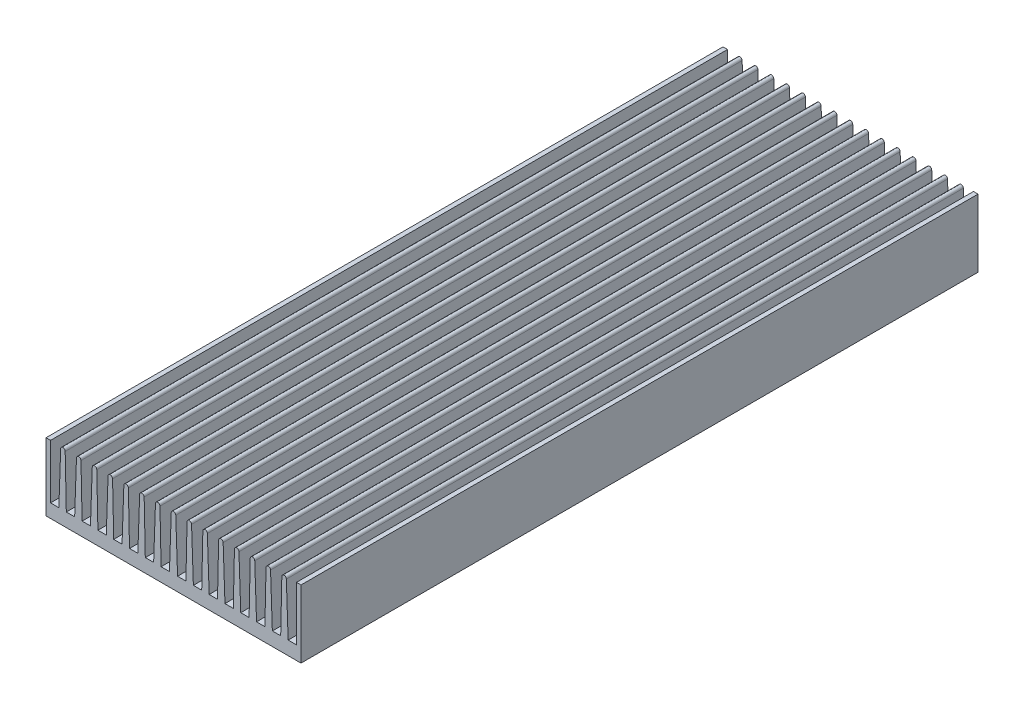
SolidWorks part; units mm, degrees
ref_plane "Plano frontal" through (0, 0, 0) normal (0, 0, 1) x (1, 0, 0)
ref_plane "Plano superior" through (0, 0, 0) normal (0, 1, 0) x (1, 0, 0)
ref_plane "Plano direito" through (0, 0, 0) normal (1, 0, 0) x (0, 0, -1)
sketch "Esboço1" plane through (0, 0, 0) normal (0, 0, 1) x (1, 0, 0)
  line L3 (0, 0) -> (-113, 0)
  line L102 (-76, 6) -> (-72.3, 6)
  line L103 (-83, 6) -> (-79.3, 6)
  line L104 (-86.3, 6) -> (-90, 6)
  line L115 (-56.5, 0) -> (-56.5, 30) construction
  line L116 (-113, 30) -> (15.3408, 30) construction
  line L146 (-86.3, 6) -> (-85.5, 29)
  line L147 (-83.5, 29) -> (-83, 6)
  line L148 (-85.5, 29) -> (-83.5, 29) construction
  line L149 (-90, 6) -> (-90.5, 29)
  line L150 (-92.5, 29) -> (-93.3, 6)
  line L151 (-48.5, 29) -> (-50.5, 29) construction
  line L152 (-93.3, 6) -> (-97, 6)
  line L153 (-97, 6) -> (-97.5, 29)
  line L154 (-99.5, 29) -> (-100.3, 6)
  line L155 (-79.3, 6) -> (-78.5, 29)
  line L156 (-76.5, 29) -> (-76, 6)
  line L161 (-78.5, 29) -> (-76.5, 29) construction
  line L162 (-72.3, 6) -> (-71.5, 29)
  line L163 (-100.3, 6) -> (-104, 6)
  line L164 (-71.5, 29) -> (-69.5, 29) construction
  line L165 (-69.5, 29) -> (-69, 6)
  line L167 (-104, 6) -> (-104.5, 29)
  line L169 (-8.5, 29) -> (-6.5, 29) construction
  line L170 (-90.5, 29) -> (-92.5, 29) construction
  line L171 (-97.5, 29) -> (-99.5, 29) construction
  line L172 (-104.5, 29) -> (-106.5, 29) construction
  line L173 (-15.5, 29) -> (-13.5, 29) construction
  line L174 (-22.5, 29) -> (-20.5, 29) construction
  line L175 (-107.3, 6) -> (-106.5, 29)
  line L176 (-113, 0) -> (-113, 30)
  line L177 (-113, 30) -> (-111, 30)
  line L178 (-111, 30) -> (-111, 6)
  line L179 (-111, 6) -> (-107.3, 6)
  line L181 (-57.5, 29) -> (-55.5, 29) construction
  line L183 (-69, 6) -> (-65.3, 6)
  line L184 (-65.3, 6) -> (-64.5, 29)
  line L185 (-64.5, 29) -> (-62.5, 29) construction
  line L186 (-62.5, 29) -> (-62, 6)
  line L187 (-62, 6) -> (-58.3, 6)
  line L188 (-58.3, 6) -> (-57.5, 29)
  line L189 (-41.5, 29) -> (-43.5, 29) construction
  line L190 (-34.5, 29) -> (-36.5, 29) construction
  line L191 (-27.5, 29) -> (-29.5, 29) construction
  line L192 (-54.7, 6) -> (-55.5, 29)
  line L193 (-51, 6) -> (-54.7, 6)
  line L194 (-50.5, 29) -> (-51, 6)
  line L195 (-47.7, 6) -> (-48.5, 29)
  line L196 (-44, 6) -> (-47.7, 6)
  line L197 (-2, 6) -> (-5.7, 6)
  line L198 (-2, 30) -> (-2, 6)
  line L199 (0, 30) -> (-2, 30)
  line L200 (0, 0) -> (0, 30)
  line L201 (-5.7, 6) -> (-6.5, 29)
  line L202 (-9, 6) -> (-8.5, 29)
  line L203 (-43.5, 29) -> (-44, 6)
  line L204 (-12.7, 6) -> (-9, 6)
  line L205 (-40.7, 6) -> (-41.5, 29)
  line L206 (-36.5, 29) -> (-37, 6)
  line L207 (-33.7, 6) -> (-34.5, 29)
  line L208 (-13.5, 29) -> (-12.7, 6)
  line L209 (-16, 6) -> (-15.5, 29)
  line L210 (-19.7, 6) -> (-16, 6)
  line L211 (-20.5, 29) -> (-19.7, 6)
  line L212 (-23, 6) -> (-22.5, 29)
  line L213 (-29.5, 29) -> (-30, 6)
  line L214 (-26.7, 6) -> (-27.5, 29)
  line L215 (-26.7, 6) -> (-23, 6)
  line L216 (-30, 6) -> (-33.7, 6)
  line L217 (-37, 6) -> (-40.7, 6)
  arc A4 (-85.5, 29) -> (-83.5, 29) centre (-84.5, 29) cw
  arc A6 (-78.5, 29) -> (-76.5, 29) centre (-77.5, 29) cw
  arc A8 (-71.5, 29) -> (-69.5, 29) centre (-70.5, 29) cw
  arc A20 (-90.5, 29) -> (-92.5, 29) centre (-91.5, 29) ccw
  arc A21 (-99.5, 29) -> (-97.5, 29) centre (-98.5, 29) cw
  arc A22 (-106.5, 29) -> (-104.5, 29) centre (-105.5, 29) cw
  arc A29 (-57.5, 29) -> (-55.5, 29) centre (-56.5, 29) cw
  arc A30 (-64.5, 29) -> (-62.5, 29) centre (-63.5, 29) cw
  arc A31 (-48.5, 29) -> (-50.5, 29) centre (-49.5, 29) ccw
  arc A32 (-6.5, 29) -> (-8.5, 29) centre (-7.5, 29) ccw
  arc A33 (-13.5, 29) -> (-15.5, 29) centre (-14.5, 29) ccw
  arc A34 (-22.5, 29) -> (-20.5, 29) centre (-21.5, 29) cw
  arc A35 (-41.5, 29) -> (-43.5, 29) centre (-42.5, 29) ccw
  arc A36 (-34.5, 29) -> (-36.5, 29) centre (-35.5, 29) ccw
  arc A37 (-27.5, 29) -> (-29.5, 29) centre (-28.5, 29) ccw
  point P43 (-56.5, 30)
  dimension "D2" = 1
  dimension "D1" = 7
  dimension "D3" = 3.7
  dimension "D4" = 2
  dimension "D5" = 6
  dimension "D6" = 113
  dimension "D8" = 30
extrude "Ressalto-extrusão1" add sketch "Esboço1" along normal blind 300
sketch "Esboço2" plane through (0, 0, 300) normal (0, 0, 1) x (1, 0, 0)
  line L1 (-100.3, 6) -> (-104, 6) construction
  line L5 (-102.5538, 0) -> (-10.4462, 0) construction
  line L23 (-9.4462, 1.7321) -> (-10.4462, 0)
  line L27 (-113, 0) -> (0, 0) construction
  line L28 (-10.4462, 0) -> (0, 0)
  line L29 (0, 0) -> (0, 41.1346)
  line L30 (0, 41.1346) -> (-6.9821, 41.1346)
  line L31 (-6.9821, 41.1346) -> (-6.9821, 6)
  line L34 (-6.9821, 6) -> (-8.4462, 3.4641)
  line L35 (-8.4462, 3.4641) -> (-7.5801, 2.9641)
  line L36 (-7.5801, 2.9641) -> (-8.5801, 1.2321)
  line L37 (-8.5801, 1.2321) -> (-9.4462, 1.7321)
  line L38 (-102.5538, 0) -> (-103.5538, 1.7321)
  line L40 (-103.5538, 1.7321) -> (-101.3888, 2.9821)
  line L41 (-101.3888, 2.9821) -> (-102.3888, 4.7141)
  line L43 (-102.3888, 4.7141) -> (-104.5538, 3.4641)
  line L45 (-104.5538, 3.4641) -> (-106.0179, 6)
  line L48 (-106.0179, 6) -> (-106.0179, 31.5406)
  line L49 (-106.0179, 31.5406) -> (-125.5568, 31.5406)
  line L50 (-125.5568, 31.5406) -> (-125.5568, -3.4367)
  line L51 (-125.5568, -3.4367) -> (-107.9645, -3.4367)
  line L52 (-107.9645, -3.4367) -> (-102.5538, 0)
  point P13 (-56.5, 0)
  point P14 (-56.5, 0)
  dimension "D1" = 92.1077
  dimension "D2" = 2
  dimension "D3" = 120
  dimension "D4" = 120
  dimension "D5" = 2
  dimension "D6" = 2
  dimension "D7" = 2
  dimension "D8" = 1
  dimension "D9" = 2.5
extrude "Corte-extrusão1" [suppressed] cut sketch "Esboço2" against normal through all both and the other way through all
sketch "Esboço3" plane through (0, 0, 300) normal (0, 0, 1) x (1, 0, 0)
  line L1 (-97, 6) -> (-122.3763, 6)
  line L2 (-97, 6) -> (-97, 40.0777)
  line L3 (-97, 40.0777) -> (-122.3763, 40.0777)
  line L4 (-122.3763, 6) -> (-122.3763, 40.0777)
  line L5 (-16, 6) -> (6.6432, 6)
  line L6 (-16, 6) -> (-16, 36.7002)
  line L7 (-16, 36.7002) -> (6.6432, 36.7002)
  line L8 (6.6432, 6) -> (6.6432, 36.7002)
extrude "Corte-extrusão2" [suppressed] cut sketch "Esboço3" against normal through all both and the other way through all
sketch "Esboço4" plane through (0, 0, 300) normal (0, 0, 1) x (1, 0, 0)
  line L0 (-56.5, 30) -> (-56.5, 0) construction
  line L1 (-113, 0) -> (0, 0) construction
  line L2 (-86.5, 3.2348) -> (-56.5, 3.2348) construction
  line L3 (-56.5, 3.2348) -> (-26.5, 3.2348) construction
  circle A0 centre (-26.5, 3.2348) radius 1.25
  circle A1 centre (-86.5, 3.2348) radius 1.25
  arc A2 (-55.5, 29) -> (-57.5, 29) centre (-56.5, 29) ccw construction
  dimension "D3" = 2.5
  dimension "D1" = 30
  dimension "D2" = 3.2348
extrude "Corte-extrusão3" [suppressed] cut sketch "Esboço4" against normal blind 10
sketch "Esboço5" [suppressed] plane through (0, 6, 0) normal (0, 1, 0) x (1, 0, 0)
  line L0 (-99.0329, -274.5) -> (-99.0329, -208.5) construction
  line L1 (-99.0329, -208.5) -> (-99.0329, -142.5) construction
  line L2 (-99.0329, -142.5) -> (-99.0329, -76.5) construction
  line L3 (-99.0329, -76.5) -> (-99.0329, -10.5) construction
  line L4 (-106.0179, 0) -> (-106.0179, -285) construction
  line L5 (-93.3, -285) -> (-106.0179, -285) construction
  circle A0 centre (-99.0329, -274.5) radius 1.25
  circle A1 centre (-99.0329, -208.5) radius 1.25
  circle A2 centre (-99.0329, -142.5) radius 1.25
  circle A3 centre (-99.0329, -76.5) radius 1.25
  circle A4 centre (-99.0329, -10.5) radius 1.25
  circle A5 centre (-12.4646, -20.5) radius 1.25
  circle A6 centre (-12.4646, -101.8333) radius 1.25
  circle A7 centre (-12.4646, -183.1667) radius 1.25
  circle A8 centre (-12.4646, -264.5) radius 1.25
  dimension "D1" = 2.5
  dimension "D3" = 10.5
  dimension "D2" = 6.985
  dimension "D4" = 66
extrude "Corte-extrusão4" [suppressed] cut sketch "Esboço5" against normal blind 5
sketch "Esboço6" [suppressed] plane through (0, 0, 0) normal (0, 0, -1) x (-1, 0, 0)
  line L0 (6.9821, 6) -> (10.4462, 0) construction
  line L1 (8.7141, 3) -> (104.2859, 3) construction
  line L2 (102.5538, 0) -> (106.0179, 6) construction
  line L3 (103.7085, 2) -> (9.2915, 2)
  line L4 (9.2915, 2) -> (8.1368, 4)
  line L5 (8.1368, 4) -> (104.8632, 4)
  line L6 (104.8632, 4) -> (103.7085, 2)
  line L7 (104.5538, 3.4641) -> (106.0179, 6) construction
  line L8 (6.9821, 6) -> (8.4462, 3.4641) construction
  line L9 (6.9821, 6) -> (19.7, 6) construction
  point P11 (104.2859, 3)
  dimension "D1" = 1
  dimension "D2" = 1
extrude "Ressalto-extrusão2" [suppressed] add sketch "Esboço6" along normal blind 1
sketch "Esboço7" plane through (0, 0, 0) normal (0, -1, 0) x (-1, 0, 0)
  circle A0 centre (95, -28.5) radius 1.65
  circle A1 centre (71.949, -28.592) radius 1.25
  circle A2 centre (72.33, -10.685) radius 1.25
  circle A3 centre (30.928, -51.5) radius 1.25
  circle A4 centre (24, -15) radius 1.65
  circle A5 centre (34.738, -79.011) radius 1.25
  circle A6 centre (18.355, -144.416) radius 1.65
  circle A7 centre (20, -249) radius 1.65
  circle A8 centre (35.246, -237) radius 1.25
  circle A9 centre (93, -249) radius 1.65
  circle A10 centre (78.807, -182.77) radius 1.25
  circle A11 centre (82.363, -100.093) radius 1.25
  circle A12 centre (29.404, -176.293) radius 1.25
  circle A13 centre (39, -220) radius 1.25
  circle A14 centre (39, -200) radius 1.25
  circle A15 centre (39, -180) radius 1.25
  circle A16 centre (39, -160) radius 1.25
  circle A17 centre (74, -130) radius 1.25
  circle A18 centre (74, -110) radius 1.25
  circle A19 centre (74, -90) radius 1.25
  circle A20 centre (74, -70) radius 1.25
  dimension "D1" = 3.3
  dimension "D2" = 2.5
extrude "Corte-extrusão5" [suppressed] cut sketch "Esboço7" against normal blind 4
